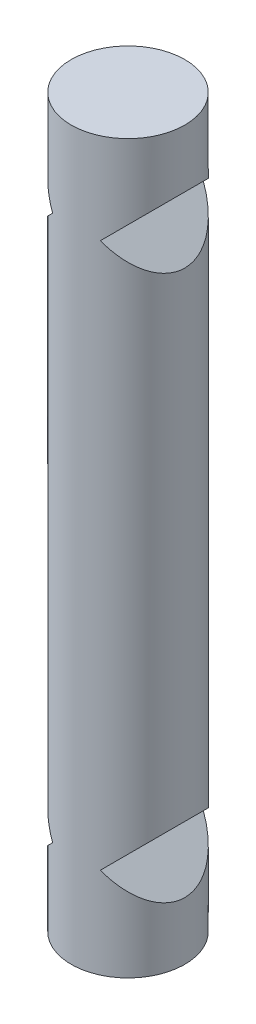
SolidWorks part; units mm, degrees
ref_plane "Front Plane" through (0, 0, 0) normal (0, 0, 1) x (1, 0, 0)
ref_plane "Top Plane" through (0, 0, 0) normal (0, 1, 0) x (1, 0, 0)
ref_plane "Right Plane" through (0, 0, 0) normal (1, 0, 0) x (0, 0, -1)
sketch "Sketch1" plane through (0, 0, 0) normal (0, 1, 0) x (1, 0, 0)
  circle A0 centre (0, 0) radius 1.25
  dimension "D1" = 2.5
extrude "Boss-Extrude1" add sketch "Sketch1" along normal blind 6
sketch "Sketch2" plane through (0, 0, 0) normal (0, -1, 0) x (1, 0, 0)
  circle A0 centre (0, 0) radius 1.25
extrude "Boss-Extrude2" add sketch "Sketch2" along normal blind 5
sketch "Sketch3" plane through (0, 6, 0) normal (0, 1, 0) x (1, 0, 0)
  circle A0 centre (0, 0) radius 1.25
extrude "Boss-Extrude3" add sketch "Sketch3" along normal blind 5
sketch "Sketch4" plane through (0, 0, 0) normal (0, 0, 1) x (1, 0, 0)
  line L0 (-1.25, 3) -> (1.25, 3) construction
  line L1 (-1.25, 11) -> (-1.25, -5) construction
  line L2 (1.25, -5) -> (1.25, 11) construction
  line L3 (1.25, 3) -> (1.25, 11) construction
  line L4 (1.25, 11) -> (1.25, 7) construction
  line L5 (1.25, 7) -> (-1.25, 7) construction
  line L6 (1.25, 7) -> (1.25, 11) construction
  line L7 (1.25, 11) -> (1.25, 9) construction
  line L8 (1.25, 9) -> (-1.25, 9) construction
  line L9 (0.5248, 9) -> (1.25, 9.7252)
  line L10 (0, 11) -> (0, -5) construction
  line L11 (1.25, 11) -> (-1.25, 11) construction
  line L12 (-1.25, -5) -> (1.25, -5) construction
  line L13 (0.5248, 9) -> (1.25, 8.2748)
  line L14 (-0.5248, 9) -> (-1.25, 8.2748)
  line L15 (-0.5248, 9) -> (-1.25, 9.7252)
  line L16 (-0.5248, -3) -> (-1.25, -3.7252)
  line L17 (-0.5248, -3) -> (-1.25, -2.2748)
  line L18 (0.5248, -3) -> (1.25, -2.2748)
  line L19 (0.5248, -3) -> (1.25, -3.7252)
  line L20 (1.25, 9.7252) -> (1.25, 8.2748)
  line L21 (-1.25, 9.7252) -> (-1.25, 8.2748)
  line L22 (-1.25, -2.2748) -> (-1.25, -3.7252)
  line L23 (1.25, -2.2748) -> (1.25, -3.7252)
  dimension "D1" = 45
extrude "Cut-Extrude1" cut sketch "Sketch4" against normal through all both and the other way through all
